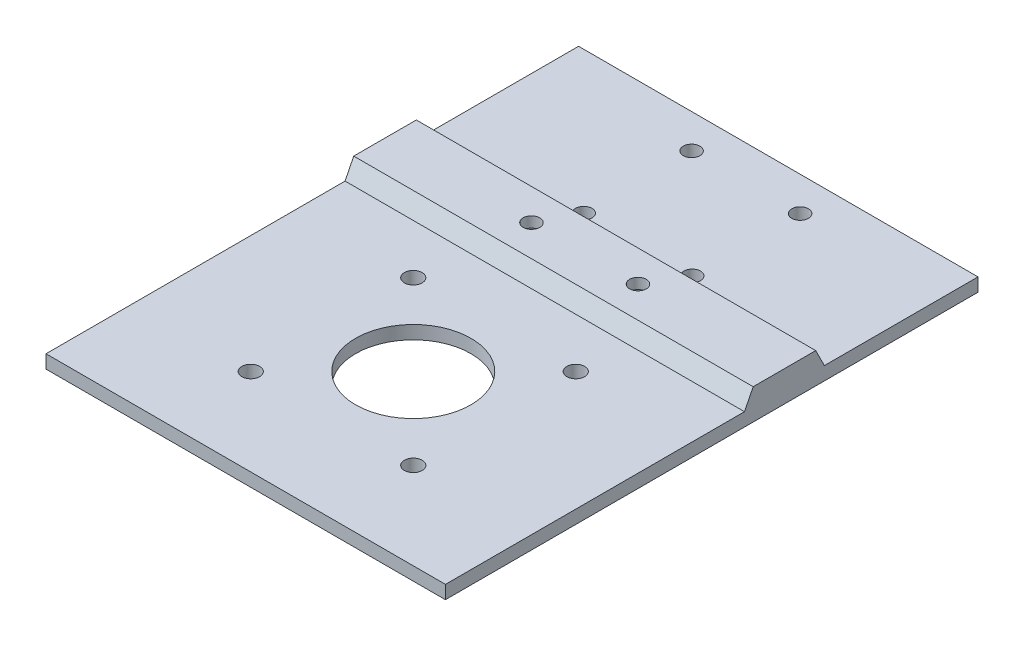
SolidWorks part; units mm, degrees
ref_plane "Front Plane" through (0, 0, 0) normal (0, 0, 1) x (1, 0, 0)
ref_plane "Top Plane" through (0, 0, 0) normal (0, 1, 0) x (1, 0, 0)
ref_plane "Right Plane" through (0, 0, 0) normal (1, 0, 0) x (0, 0, -1)
sketch "Sketch1" plane through (0, 0, 0) normal (0, 1, 0) x (1, 0, 0)
  line L1 (-38.1, -50.8) -> (38.1, -50.8)
  line L2 (-38.1, -50.8) -> (-38.1, 50.8)
  line L3 (-38.1, 50.8) -> (38.1, 50.8)
  line L4 (38.1, -50.8) -> (38.1, 50.8)
  line L5 (-38.1, -50.8) -> (38.1, 50.8) construction
  line L6 (-38.1, 50.8) -> (38.1, -50.8) construction
  point P0 (0, 0)
  dimension "D1" = 76.2
  dimension "4in" = 101.6
extrude "Boss-Extrude1" add sketch "Sketch1" along normal blind 2.54
sketch "Sketch2" plane through (0, 2.54, 0) normal (0, 1, 0) x (1, 0, 0)
  line L0 (-10.0338, 44.2921) -> (10.6672, 44.2921) construction
  line L1 (10.6672, 44.2921) -> (10.6672, 23.7166) construction
  line L2 (10.6672, 23.7166) -> (-10.0338, 23.7166) construction
  line L3 (-10.0338, 23.7166) -> (-10.0338, 44.2921) construction
  line L4 (-15.63, -3.2078) -> (15.3707, -3.2078) construction
  line L5 (15.3707, -3.2078) -> (15.3707, -34.2085) construction
  line L6 (15.3707, -34.2085) -> (-15.63, -34.2085) construction
  line L7 (-15.63, -34.2085) -> (-15.63, -3.2078) construction
  line L8 (-15.63, -3.2078) -> (15.3707, -34.2085) construction
  line L9 (15.3707, -3.2078) -> (-15.63, -34.2085) construction
  circle A0 centre (-10.0338, 44.2921) radius 1.5875
  circle A1 centre (10.6672, 44.2921) radius 1.5875
  circle A2 centre (10.6672, 23.7166) radius 1.5875
  circle A3 centre (-10.0338, 23.7166) radius 1.5875
  circle A4 centre (-15.63, -3.2078) radius 1.7005
  circle A5 centre (15.3707, -3.2078) radius 1.7005
  circle A6 centre (15.3707, -34.2085) radius 1.7005
  circle A7 centre (-15.63, -34.2085) radius 1.7005
  circle A8 centre (-0.1296, -18.7082) radius 10.9995
  point P18 (-0.1296, -18.7082)
  dimension "D1" = 3.175
  dimension "D4" = 31.0007
  dimension "D5" = 3.4011
  dimension "D6" = 21.9989
  dimension "D2" = 20.701
  dimension "D3" = 20.5755
extrude "Cut-Extrude1" cut sketch "Sketch2" against normal up to surface (2.54 mm away) up to face at (0, 0, 0)
sketch "Sketch3" plane through (-38.1, 0, -50.8) normal (1, 0, 0) x (0, 0, -1)
  line L0 (-44.5459, 2.54) -> (-29.3059, 2.54)
  line L2 (-29.3059, 2.54) -> (-30.9569, 5.842)
  line L3 (-30.9569, 5.842) -> (-42.8949, 5.842)
  line L4 (-42.8949, 5.842) -> (-44.5459, 2.54)
  line L5 (0, 2.54) -> (-101.6, 2.54) construction
  point P7 (-36.9259, 2.54)
  dimension "D1" = 15.24
  dimension "D2" = 11.938
  dimension "D3" = 3.302
  dimension "D4" = 11.43
extrude "Boss-Extrude2" add sketch "Sketch3" along normal up to surface (76.2 mm away) contours L3 L4 L0 L2 up to face at (38.1, 1.27, 0)
sketch "Sketch4" plane through (0, 0, 0) normal (0, -1, 0) x (1, 0, 0)
  line L0 (-10.16, -13.8741) -> (10.16, -13.8741) construction
  line L1 (0, -13.8741) -> (0, 0) construction
  line L2 (38.1, -7.9051) -> (-38.1, -7.9051) construction
  line L3 (38.1, -19.8431) -> (-38.1, -19.8431) construction
  circle A0 centre (-10.16, -13.8741) radius 3.175
  circle A1 centre (10.16, -13.8741) radius 3.175
  dimension "D2" = 6.35
  dimension "D1" = 20.32
extrude "Cut-Extrude2" cut sketch "Sketch4" along direction (0, -1, 0) on the side against the normal blind 3.81
sketch "Sketch5" plane through (0, 3.81, 0) normal (0, -1, 0) x (1, 0, 0)
  circle A2 centre (-10.0338, -23.7166) radius 1.5875 construction
  circle A3 centre (-10.16, -13.8741) radius 3.175 construction
  circle A4 centre (-10.16, -13.8741) radius 1.5875
  circle A6 centre (10.16, -13.8741) radius 1.5875
  circle A7 centre (10.16, -13.8741) radius 3.175 construction
extrude "Cut-Extrude3" cut sketch "Sketch5" against normal through all
